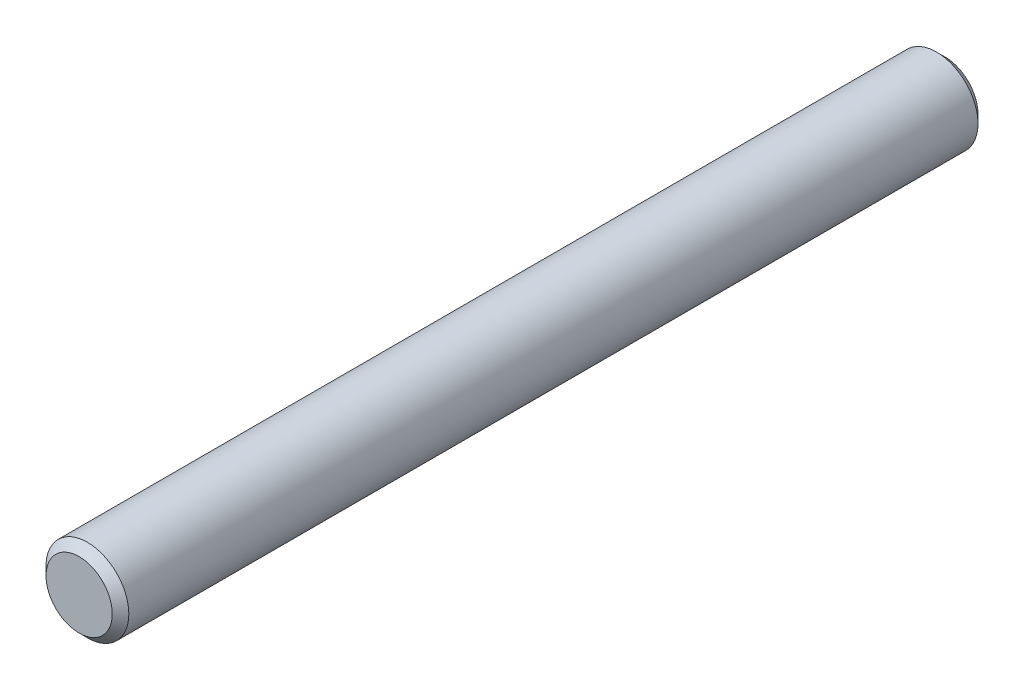
SolidWorks part; units mm, degrees
material "Plain Carbon Steel"
ref_plane "Front" through (0, 0, 0) normal (0, 0, 1) x (1, 0, 0)
ref_plane "Top" through (0, 0, 0) normal (0, 1, 0) x (1, 0, 0)
ref_plane "Right" through (0, 0, 0) normal (1, 0, 0) x (0, 0, -1)
sketch "Sketch1" plane through (0, 0, 0) normal (0, 0, 1) x (1, 0, 0)
  circle A0 centre (0, 0) radius 4.7625
  dimension "dia" = 9.525
extrude "Extrude1" add sketch "Sketch1" along normal mid plane 99.568
sketch "Sketch2" plane through (0, 0, 0) normal (1, 0, 0) x (0, 0, -1)
  line L0 (49.784, 4.7625) -> (47.244, 4.7625) construction
  line L1 (49.784, 4.7625) -> (-49.784, 4.7625) construction
  line L2 (47.244, 4.7625) -> (42.3088, 4.7625) construction
  line L3 (42.3088, 4.7625) -> (32.3012, 4.7625) construction
  line L4 (32.3012, 4.7625) -> (27.366, 4.7625) construction
  line L8 (37.305, 4.7625) -> (37.305, -4.7625) construction
  line L9 (-49.784, -4.7625) -> (49.784, -4.7625) construction
  line L10 (27.366, 4.7625) -> (17.3584, 4.7625) construction
  line L11 (17.3584, 4.7625) -> (12.4231, 4.7625) construction
  line L12 (12.4231, 4.7625) -> (2.4155, 4.7625) construction
  line L13 (2.4155, 4.7625) -> (-2.5197, 4.7625) construction
  line L14 (-2.5197, 4.7625) -> (-12.5273, 4.7625) construction
  line L15 (24.826, 4.7625) -> (24.826, -4.7625) construction
  line L16 (9.8831, 4.7625) -> (9.8831, -4.7625) construction
  line L17 (-5.0597, 4.7625) -> (-5.0597, -4.7625) construction
  line L18 (-12.5273, 4.7625) -> (-17.4625, 4.7625) construction
  line L19 (34.8412, 4.7625) -> (39.7688, 4.7625) construction
  line L20 (34.8412, 4.7625) -> (34.8412, -4.7625) construction
  line L21 (34.8412, -4.7625) -> (39.7688, -4.7625) construction
  line L22 (39.7688, 4.7625) -> (39.7688, -4.7625) construction
  line L23 (-17.4625, 4.7625) -> (-27.4701, 4.7625) construction
  line L24 (-27.4701, 4.7625) -> (-32.4053, 4.7625) construction
  line L25 (-32.4053, 4.7625) -> (-42.4129, 4.7625) construction
  line L26 (-42.4129, 4.7625) -> (-47.3405, 4.7625) construction
  line L27 (-20.0025, 4.7625) -> (-20.0025, -4.7625) construction
  line L28 (-34.9453, 4.7625) -> (-34.9453, -4.7625) construction
  point P0 (-49.784, 4.7625)
  point P1 (49.784, 4.7625)
  point P30 (37.305, 4.7625)
  dimension "D1" = 2.54
  dimension "D2" = 4.9352
  dimension "D3" = 10.0076
  dimension "D4" = 4.9352
  dimension "D5" = 10.0076
  dimension "D6" = 4.9352
  dimension "D7" = 10.0076
  dimension "D8" = 4.9352
  dimension "D9" = 10.0076
  dimension "D10" = 4.9276
  dimension "D11" = 2.54
  dimension "D12" = 2.54
  dimension "D13" = 2.54
  dimension "D14" = 4.9352
  dimension "D15" = 4.9352
  dimension "D16" = 10.0076
  dimension "D17" = 10.0076
  dimension "D18" = 4.9276
  dimension "D19" = 2.54
  dimension "D20" = 2.54
chamfer "Chamfer1" distance 0.9525 angle 45 2 edges at (4.7625, 0, -49.784) (4.7625, 0, 49.784)
equation "\"D1@Chamfer1\" = \"dia@Sketch1\" * .1"
